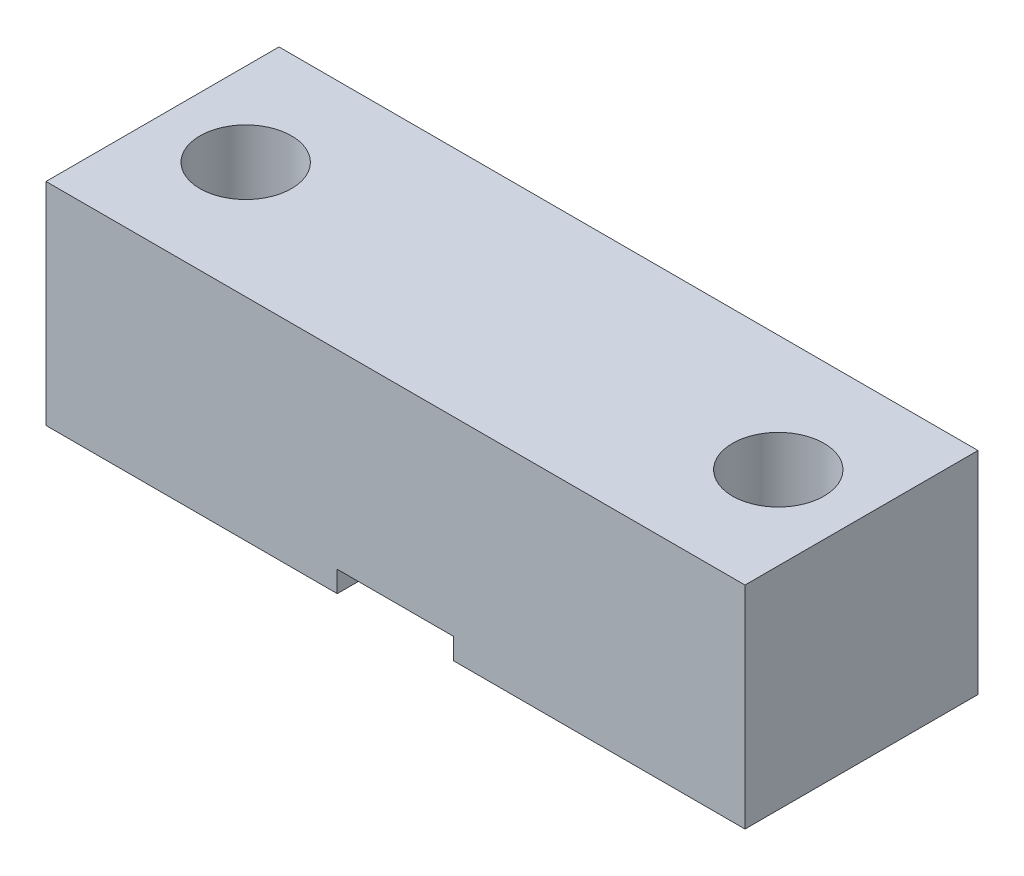
SolidWorks part; units mm, degrees
ref_plane "Front Plane" through (0, 0, 0) normal (0, 0, 1) x (1, 0, 0)
ref_plane "Top Plane" through (0, 0, 0) normal (0, 1, 0) x (1, 0, 0)
ref_plane "Right Plane" through (0, 0, 0) normal (1, 0, 0) x (0, 0, -1)
sketch "Sketch1" plane through (0, 0, 0) normal (0, 1, 0) x (1, 0, 0)
  line L1 (-21, 7) -> (21, 7)
  line L2 (-21, 7) -> (-21, -7)
  line L3 (-21, -7) -> (21, -7)
  line L4 (21, 7) -> (21, -7)
  line L5 (-21, 7) -> (21, -7) construction
  line L6 (-21, -7) -> (21, 7) construction
  circle A0 centre (-16, 0) radius 2.75
  circle A1 centre (16, 0) radius 2.75
  point P4 (0, 0)
  dimension "D3" = 5.5
  dimension "D1" = 14
  dimension "D2" = 42
  dimension "D4" = 32
  dimension "D5" = 16
extrude "Boss-Extrude1" add sketch "Sketch1" along normal blind 12.7
sketch "Sketch2" plane through (0, 0, 7) normal (0, 0, 1) x (1, 0, 0)
  line L0 (-21, 0) -> (21, 0) construction
  line L1 (-3.5, 1.27) -> (3.5, 1.27)
  line L2 (-3.5, 1.27) -> (-3.5, 0)
  line L3 (-3.5, 0) -> (3.5, 0)
  line L4 (3.5, 1.27) -> (3.5, 0)
  point P4 (0, 0)
  point P7 (0, 0)
  dimension "D1" = 7
  dimension "D2" = 1.27
extrude "Cut-Extrude1" cut sketch "Sketch2" against normal up to surface (14 mm away) up to face at (0, 6.35, -7)
